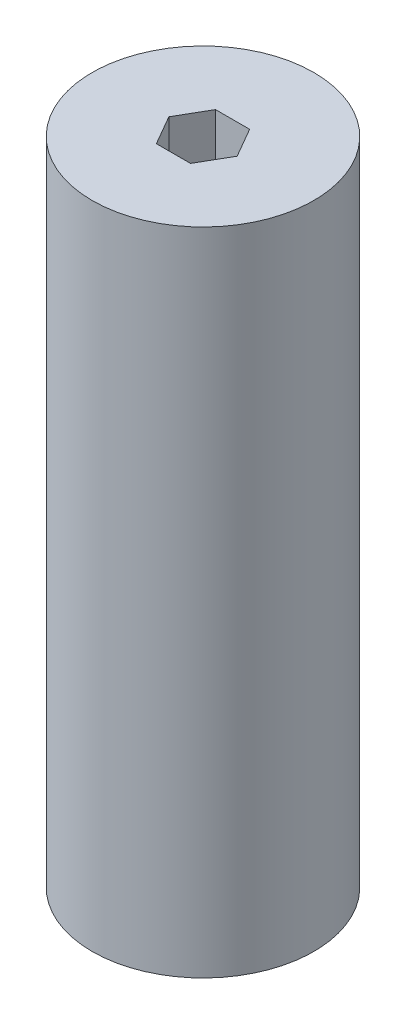
SolidWorks part; units mm, degrees
ref_plane "Front Plane" through (0, 0, 0) normal (0, 0, 1) x (1, 0, 0)
ref_plane "Top Plane" through (0, 0, 0) normal (0, 1, 0) x (1, 0, 0)
ref_plane "Right Plane" through (0, 0, 0) normal (1, 0, 0) x (0, 0, -1)
sketch "Sketch1" plane through (0, 0, 0) normal (0, 1, 0) x (1, 0, 0)
  line L1 (3.6662, -6.35) -> (7.3323, 0)
  line L2 (7.3323, 0) -> (3.6662, 6.35)
  line L3 (3.6662, 6.35) -> (-3.6662, 6.35)
  line L4 (-3.6662, 6.35) -> (-7.3323, 0)
  line L5 (-7.3323, 0) -> (-3.6662, -6.35)
  line L6 (-3.6662, -6.35) -> (3.6662, -6.35)
  circle A0 centre (0, 0) radius 23.8125
  circle A1 centre (0, 0) radius 6.35 construction
  dimension "D1" = 47.625
  dimension "D2" = 12.7
extrude "Boss-Extrude1" add sketch "Sketch1" along normal blind 139.7
